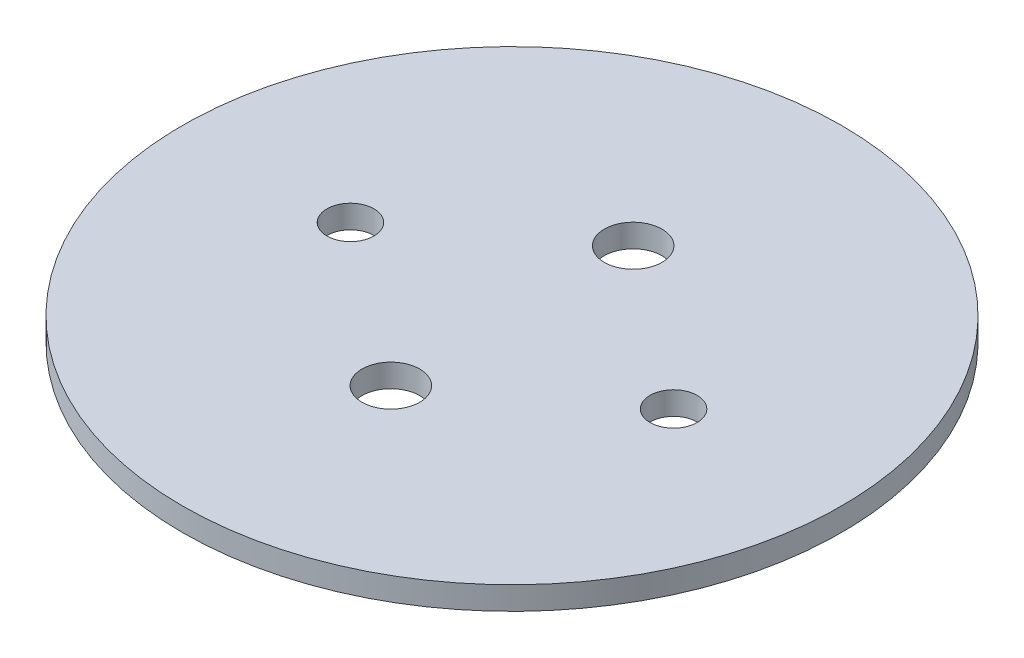
SolidWorks part; units mm, degrees
ref_plane "Front Plane" through (0, 0, 0) normal (0, 0, 1) x (1, 0, 0)
ref_plane "Top Plane" through (0, 0, 0) normal (0, 1, 0) x (1, 0, 0)
ref_plane "Right Plane" through (0, 0, 0) normal (1, 0, 0) x (0, 0, -1)
sketch "Sketch1" plane through (0, 0, 0) normal (0, 1, 0) x (1, 0, 0)
  line L0 (-22.225, 0) -> (22.225, 0) construction
  line L1 (0, 16.6687) -> (0, -16.6687) construction
  circle A0 centre (0, 0) radius 45.339
  circle A1 centre (22.225, 0) radius 3.2385
  circle A2 centre (-22.225, 0) radius 3.2385
  circle A3 centre (0, 16.6687) radius 3.9687
  circle A4 centre (0, -16.6687) radius 3.9687
  point P6 (0, 0)
  point P11 (0, 0)
  dimension "D1" = 6.477
  dimension "D2" = 90.678
  dimension "D5" = 33.3375
  dimension "D4" = 7.9375
  dimension "D3" = 44.45
extrude "Boss-Extrude1" add sketch "Sketch1" along normal blind 3.175
